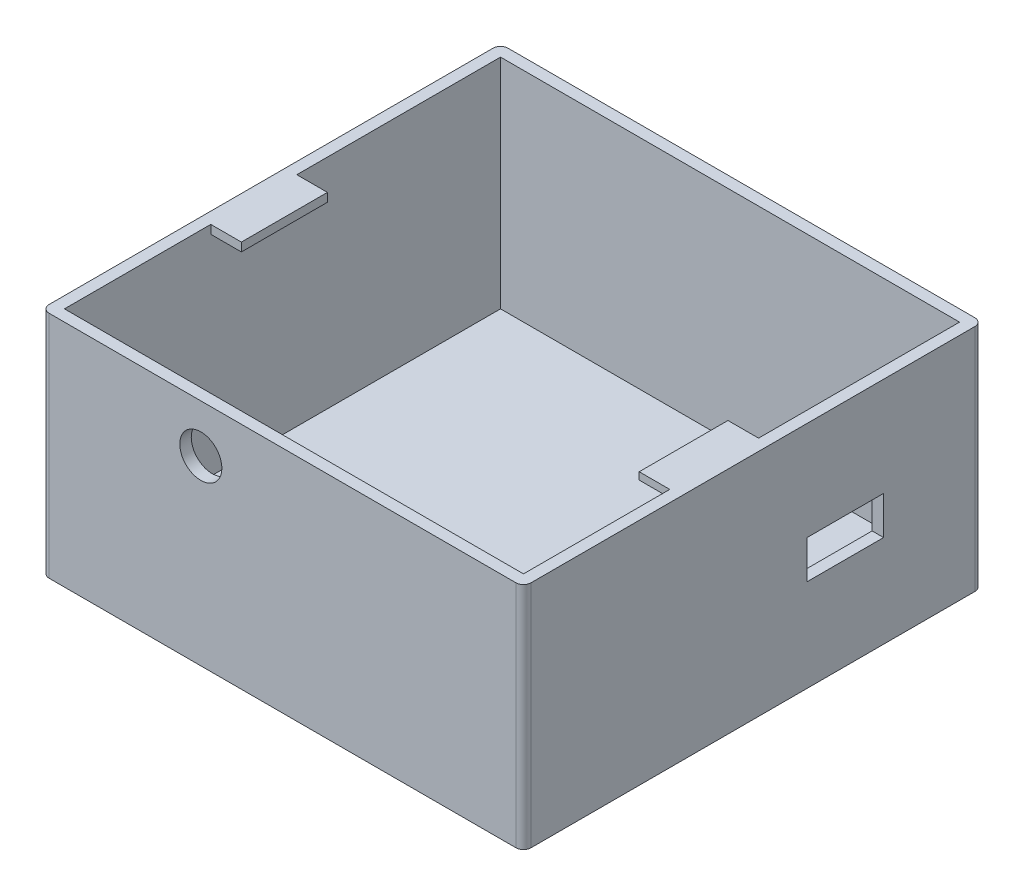
SolidWorks part; units mm, degrees
ref_plane "Front Plane" through (0, 0, 0) normal (0, 0, 1) x (1, 0, 0)
ref_plane "Top Plane" through (0, 0, 0) normal (0, 1, 0) x (1, 0, 0)
ref_plane "Right Plane" through (0, 0, 0) normal (1, 0, 0) x (0, 0, -1)
sketch "Sketch1" plane through (0, 0, 0) normal (0, 1, 0) x (1, 0, 0)
  line L1 (-23.2151, 27.2939) -> (39.7849, 27.2939)
  line L2 (-23.2151, 27.2939) -> (-23.2151, -32.7061)
  line L3 (-23.2151, -32.7061) -> (39.7849, -32.7061)
  line L4 (39.7849, 27.2939) -> (39.7849, -32.7061)
  dimension "D1" = 60
  dimension "D2" = 63
extrude "Boss-Extrude1" add sketch "Sketch1" along normal blind 30
sketch "Sketch2" plane through (0, 0, 0) normal (0, 1, 0) x (1, 0, 0)
  line L8 (-21.7151, 25.7939) -> (-21.7151, -31.2061)
  line L9 (-21.7151, -31.2061) -> (38.2849, -31.2061)
  line L10 (38.2849, -31.2061) -> (38.2849, 25.7939)
  line L11 (38.2849, 25.7939) -> (-21.7151, 25.7939)
  line L12 (-21.7151, 25.7939) -> (-21.7151, -31.2061)
  line L13 (-21.7151, -31.2061) -> (38.2849, -31.2061)
  line L14 (38.2849, -31.2061) -> (38.2849, 25.7939)
  line L15 (38.2849, 25.7939) -> (-21.7151, 25.7939)
  dimension "D1" = 1.5
extrude "Cut-Extrude1" cut sketch "Sketch2" along normal blind 44
fillet "Fillet5" radius 1 1 edges at (39.7849, 15, -27.2939)
fillet "Fillet6" radius 1 3 edges at (39.7849, 15, 32.7061) (-23.2151, 15, 32.7061) (-23.2151, 15, -27.2939)
sketch "Sketch4" plane through (-21.7151, 0, 0) normal (1, 0, 0) x (0, 0, -1)
  line L0 (-31.2061, 30) -> (25.7939, 30) construction
  line L1 (-12.0805, 30) -> (-0.8325, 30)
  line L2 (-12.0805, 30) -> (-12.0805, 28.8792)
  line L3 (-12.0805, 28.8792) -> (-0.8325, 28.8792)
  line L4 (-0.8325, 30) -> (-0.8325, 28.8792)
extrude "Boss-Extrude2" add sketch "Sketch4" along normal blind 4
sketch "Sketch7" plane through (38.2849, 0, 0) normal (-1, 0, 0) x (0, 0, 1)
  line L0 (-25.7939, 30) -> (31.2061, 30) construction
  line L1 (0.4781, 30) -> (12.0805, 30)
  line L2 (0.4781, 30) -> (0.4781, 29.0536)
  line L3 (0.4781, 29.0536) -> (12.0805, 29.0536)
  line L4 (12.0805, 30) -> (12.0805, 29.0536)
extrude "Boss-Extrude3" add sketch "Sketch7" along normal blind 4
sketch "Sketch8" plane through (0, 0, 32.7061) normal (0, 0, 1) x (1, 0, 0)
  circle A0 centre (-2.3916, 23.7451) radius 2.75
  dimension "D1" = 5.5
sketch "Sketch13" plane through (0, 0, -25.7939) normal (0, 0, 1) x (1, 0, 0)
  line L0 (-21.7151, 30) -> (-21.7151, 0) construction
  line L1 (38.2849, 0) -> (-21.7151, 0)
  line L2 (38.2849, 0) -> (38.2849, 1.5)
  line L3 (38.2849, 1.5) -> (-21.7151, 1.5)
  line L4 (-21.7151, 0) -> (-21.7151, 1.5)
  dimension "D1" = 1.5
extrude "Boss-Extrude4" add sketch "Sketch13" along normal blind 52
extrude "Cut-Extrude2" cut sketch "Sketch8" along normal blind 15 and the other way blind 20
sketch "Sketch17" plane through (39.7849, 0, 0) normal (1, 0, 0) x (0, 0, -1)
  line L0 (26.2939, 0) -> (14.3634, 0)
  line L1 (-31.7061, 0) -> (26.2939, 0) construction
  line L2 (14.3634, 0) -> (14.3634, 12.0775)
  point P5 (0, 0)
sketch "Sketch18" plane through (39.7849, 0, 0) normal (1, 0, 0) x (0, 0, -1)
  line L1 (14.3634, 12.0775) -> (4.3634, 12.0775)
  line L2 (14.3634, 12.0775) -> (14.3634, 17.0775)
  line L3 (14.3634, 17.0775) -> (4.3634, 17.0775)
  line L4 (4.3634, 12.0775) -> (4.3634, 17.0775)
  dimension "D1" = 10
  dimension "D2" = 5
extrude "Cut-Extrude4" cut sketch "Sketch18" against normal blind 15
